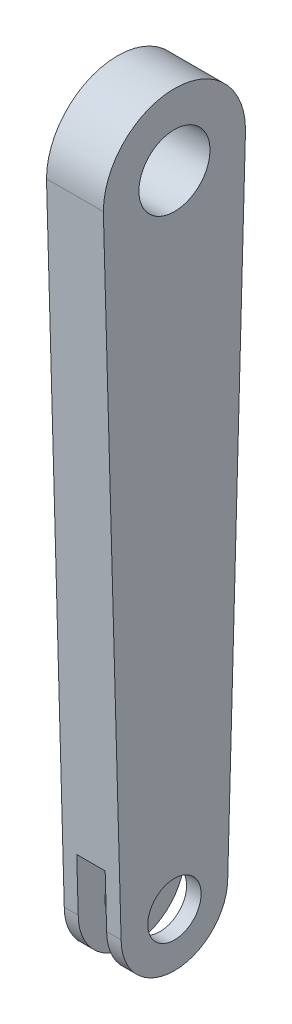
SolidWorks part; units mm, degrees
material "6061 合金"
ref_plane "前视基准面" through (0, 0, 0) normal (0, 0, 1) x (1, 0, 0)
ref_plane "上视基准面" through (0, 0, 0) normal (0, 1, 0) x (1, 0, 0)
ref_plane "右视基准面" through (0, 0, 0) normal (1, 0, 0) x (0, 0, -1)
sketch "草图1" plane through (0, 0, 0) normal (1, 0, 0) x (0, 0, -1)
  line L0 (0, 0) -> (0, -180) construction
  line L1 (20, 0) -> (15, -180)
  line L2 (-20, 0) -> (-15, -180)
  circle A0 centre (0, 0) radius 20
  circle A1 centre (0, -180) radius 15
  dimension "D1" = 40
  dimension "D2" = 30
  dimension "D3" = 180
extrude "凸台-拉伸1" add sketch "草图1" along normal blind 16
sketch "草图2" plane through (16, 0, 0) normal (1, 0, 0) x (0, 0, -1)
  circle A0 centre (0, 0) radius 10
  circle A1 centre (0, -180) radius 7.5
  dimension "D1" = 20
  dimension "D2" = 15
extrude "切除-拉伸1" cut sketch "草图2" against normal blind 16
ref_plane "基准面1" through (0, -230, 0) normal (0, 1, 0) x (1, 0, 0)
sketch "草图3" plane through (0, -230, 0) normal (0, 1, 0) x (1, 0, 0)
  line L0 (16, -20) -> (0, -20) construction
  line L1 (3.9274, 20) -> (11.9274, 20)
  line L2 (3.9274, 20) -> (3.9274, -20)
  line L3 (3.9274, -20) -> (11.9274, -20)
  line L4 (11.9274, 20) -> (11.9274, -20)
  line L5 (3.9274, 20) -> (11.9274, -20) construction
  line L6 (3.9274, -20) -> (11.9274, 20) construction
  point P0 (7.9274, 0)
  dimension "D1" = 8
extrude "切除-拉伸2" cut sketch "草图3" along normal blind 65
sketch "草图4" plane through (16, 0, 0) normal (1, 0, 0) x (0, 0, -1)
  line L0 (0, 0) -> (0, -180)
ref_plane "基准面2" through (0, 10, -17.3205) normal (0, 0.5, -0.866) x (-1, 0, 0)
